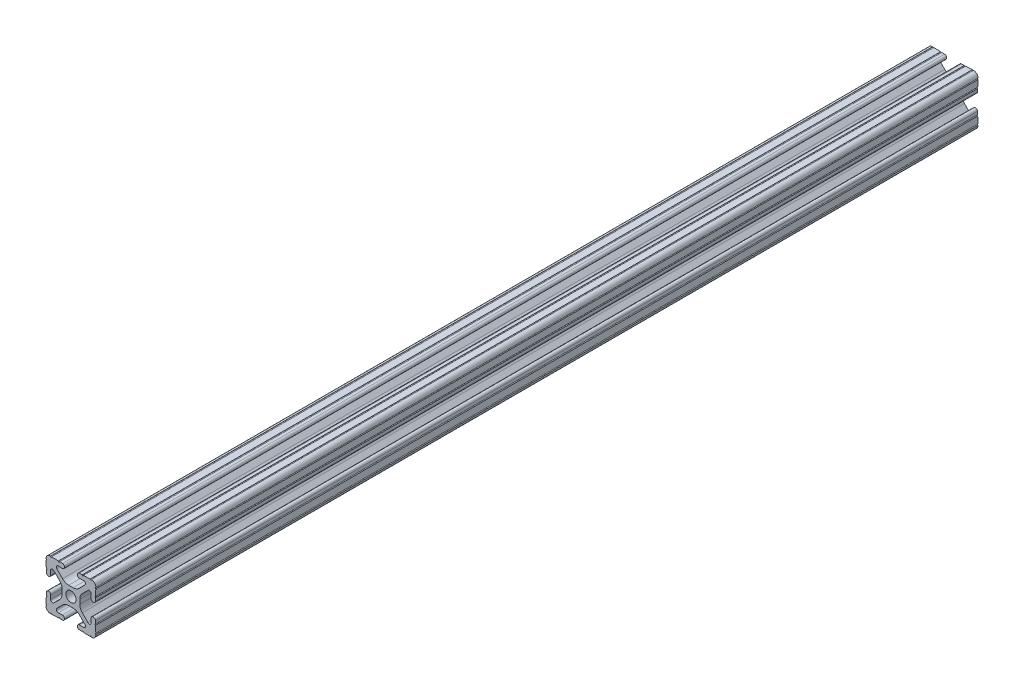
SolidWorks part; units mm, degrees
material "6063-T5"
ref_plane "Front Plane" through (0, 0, 0) normal (0, 0, 1) x (1, 0, 0)
ref_plane "Top Plane" through (0, 0, 0) normal (0, 1, 0) x (1, 0, 0)
ref_plane "Right Plane" through (0, 0, 0) normal (1, 0, 0) x (0, 0, -1)
sketch "Sketch1" plane through (0, 0, 0) normal (0, 0, 1) x (1, 0, 0)
  line L0 (0, 12.7) -> (-12.7814, 12.7) construction
  line L1 (-4.5085, 0) -> (-4.5085, 2.9459)
  line L2 (-6.0437, 12.5461) -> (-10.0976, 12.6876) construction
  line L3 (-11.5616, 12.4229) -> (-4.3159, 12.1699) construction
  line L4 (-6.4364, 10.3486) -> (-6.3592, 12.5571) construction
  line L6 (-2.9459, 4.5085) -> (0, 4.5085)
  line L7 (0, 0) -> (0, 12.7) construction
  line L8 (0, 0) -> (-12.7814, 0) construction
  line L9 (0.7813, 0.7813) -> (-0.7813, -0.7813) construction
  line L10 (-2.9459, 4.5085) -> (-7.1484, 8.711)
  line L11 (-4.5085, 2.9459) -> (-8.711, 7.1484)
  line L13 (0, 0) -> (-12.7814, 12.7814) construction
  line L14 (-10.4131, 12.6987) -> (-4.3048, 12.4853)
  line L15 (-4.3048, 12.4853) -> (-4.382, 10.2769) construction
  line L16 (-4.382, 10.2769) -> (-6.4364, 10.3486)
  line L17 (-12.6987, 10.4131) -> (-12.4853, 4.3048)
  line L18 (-10.2769, 4.382) -> (-10.3486, 6.4364)
  circle A0 centre (0, 0) radius 2.6035
  arc A1 (-4.382, 10.2769) -> (-4.3048, 12.4853) centre (-4.3434, 11.3811) ccw
  arc A2 (-7.1484, 8.711) -> (-6.4364, 10.3486) centre (-6.4698, 9.3896) cw
  arc A3 (-8.711, 7.1484) -> (-10.3486, 6.4364) centre (-9.3896, 6.4698) ccw
  arc A4 (-10.2769, 4.382) -> (-12.4853, 4.3048) centre (-11.3811, 4.3434) cw
  arc A5 (-10.4131, 12.6987) -> (-12.6987, 10.4131) centre (-10.4902, 10.4902) ccw
  arc A6 (-10.4131, 12.6987) -> (-9.7821, 12.6766) centre (-10.0976, 12.6876) ccw
  arc A7 (-6.3592, 12.5571) -> (-5.7282, 12.5351) centre (-6.0437, 12.5461) ccw
  arc A8 (-12.5571, 6.3592) -> (-12.5351, 5.7282) centre (-12.5461, 6.0437) cw
  arc A9 (-12.6987, 10.4131) -> (-12.6766, 9.7821) centre (-12.6876, 10.0976) cw
  dimension "D1" = 5.207
  dimension "D5" = 14.859
  dimension "D9" = 2
  dimension "D2" = 25.4
  dimension "D12" = 0.6314
  dimension "D10" = 2.2098
  dimension "D3" = 9.017
  dimension "D4" = 9.017
  dimension "D6" = 25.4
  dimension "D7" = 6.477
  dimension "D8" = 2.2098
  dimension "D11" = 12.7
sketch "Sketch3" plane through (0, 0, 0) normal (0, 0, 1) x (1, 0, 0)
  line L0 (-2.9459, 4.5085) -> (0, 4.5085) construction
  line L1 (-2.9459, 4.5085) -> (-7.1484, 8.711) construction
  line L2 (-4.382, 10.2769) -> (-6.4364, 10.3486) construction
  line L3 (-10.4131, 12.6987) -> (-4.3048, 12.4853) construction
  line L4 (-4.5085, 0) -> (-4.5085, 2.9459) construction
  line L5 (-4.5085, 2.9459) -> (-8.711, 7.1484) construction
  line L6 (-10.2769, 4.382) -> (-10.3486, 6.4364) construction
  line L7 (-12.6987, 10.4131) -> (-12.4853, 4.3048) construction
  line L8 (-1.1153, 4.5085) -> (1.1153, 4.5085)
  line L9 (-4.2404, 5.803) -> (-7.1484, 8.711)
  line L10 (-4.382, 10.2769) -> (-6.4364, 10.3486)
  line L11 (-9.7821, 12.6766) -> (-6.3592, 12.5571)
  line L12 (-4.5085, -1.1153) -> (-4.5085, 1.1153)
  line L13 (-5.803, 4.2404) -> (-8.711, 7.1484)
  line L14 (-10.2769, 4.382) -> (-10.3486, 6.4364)
  line L15 (-12.6766, 9.7821) -> (-12.5571, 6.3592)
  line L16 (-5.7282, 12.5351) -> (-4.3048, 12.4853)
  line L17 (-12.5351, 5.7282) -> (-12.4853, 4.3048)
  line L18 (0, 0) -> (0, 12.7) construction
  line L19 (0, 0) -> (-12.7814, 0) construction
  line L20 (12.5351, 5.7282) -> (12.4853, 4.3048)
  line L21 (5.7282, 12.5351) -> (4.3048, 12.4853)
  line L22 (12.6766, 9.7821) -> (12.5571, 6.3592)
  line L23 (10.2769, 4.382) -> (10.3486, 6.4364)
  line L24 (5.803, 4.2404) -> (8.711, 7.1484)
  line L25 (4.5085, -1.1153) -> (4.5085, 1.1153)
  line L26 (9.7821, 12.6766) -> (6.3592, 12.5571)
  line L27 (4.382, 10.2769) -> (6.4364, 10.3486)
  line L28 (4.2404, 5.803) -> (7.1484, 8.711)
  line L29 (4.2404, -5.803) -> (7.1484, -8.711)
  line L30 (4.382, -10.2769) -> (6.4364, -10.3486)
  line L31 (9.7821, -12.6766) -> (6.3592, -12.5571)
  line L32 (5.803, -4.2404) -> (8.711, -7.1484)
  line L33 (10.2769, -4.382) -> (10.3486, -6.4364)
  line L34 (12.6766, -9.7821) -> (12.5571, -6.3592)
  line L35 (5.7282, -12.5351) -> (4.3048, -12.4853)
  line L36 (12.5351, -5.7282) -> (12.4853, -4.3048)
  line L37 (-12.5351, -5.7282) -> (-12.4853, -4.3048)
  line L38 (-5.7282, -12.5351) -> (-4.3048, -12.4853)
  line L39 (-12.6766, -9.7821) -> (-12.5571, -6.3592)
  line L40 (-10.2769, -4.382) -> (-10.3486, -6.4364)
  line L41 (-5.803, -4.2404) -> (-8.711, -7.1484)
  line L42 (-9.7821, -12.6766) -> (-6.3592, -12.5571)
  line L43 (-4.382, -10.2769) -> (-6.4364, -10.3486)
  line L44 (-4.2404, -5.803) -> (-7.1484, -8.711)
  line L45 (-1.1153, -4.5085) -> (1.1153, -4.5085)
  arc A0 (-10.4131, 12.6987) -> (-9.7821, 12.6766) centre (-10.0976, 12.6876) ccw construction
  arc A1 (-6.4364, 10.3486) -> (-7.1484, 8.711) centre (-6.4698, 9.3896) ccw construction
  arc A2 (-4.382, 10.2769) -> (-4.3048, 12.4853) centre (-4.3434, 11.3811) ccw construction
  arc A3 (-8.711, 7.1484) -> (-10.3486, 6.4364) centre (-9.3896, 6.4698) ccw construction
  arc A4 (-12.4853, 4.3048) -> (-10.2769, 4.382) centre (-11.3811, 4.3434) ccw construction
  arc A5 (-6.3592, 12.5571) -> (-5.7282, 12.5351) centre (-6.0437, 12.5461) ccw construction
  arc A6 (-10.4131, 12.6987) -> (-12.6987, 10.4131) centre (-10.4902, 10.4902) ccw construction
  arc A7 (-12.6766, 9.7821) -> (-12.6987, 10.4131) centre (-12.6876, 10.0976) ccw construction
  arc A8 (-12.5351, 5.7282) -> (-12.5571, 6.3592) centre (-12.5461, 6.0437) ccw construction
  arc A9 (-10.4131, 12.6987) -> (-9.7821, 12.6766) centre (-10.0976, 12.6876) ccw
  arc A10 (-6.4364, 10.3486) -> (-7.1484, 8.711) centre (-6.4698, 9.3896) ccw
  arc A11 (-4.382, 10.2769) -> (-4.3048, 12.4853) centre (-4.3434, 11.3811) ccw
  arc A12 (-8.711, 7.1484) -> (-10.3486, 6.4364) centre (-9.3896, 6.4698) ccw
  arc A13 (-12.4853, 4.3048) -> (-10.2769, 4.382) centre (-11.3811, 4.3434) ccw
  arc A14 (-6.3592, 12.5571) -> (-5.7282, 12.5351) centre (-6.0437, 12.5461) ccw
  arc A15 (-10.4131, 12.6987) -> (-12.6987, 10.4131) centre (-10.4902, 10.4902) ccw
  arc A16 (-12.6766, 9.7821) -> (-12.6987, 10.4131) centre (-12.6876, 10.0976) ccw
  arc A17 (-12.5351, 5.7282) -> (-12.5571, 6.3592) centre (-12.5461, 6.0437) ccw
  arc A18 (-1.1153, 4.5085) -> (-4.2404, 5.803) centre (-1.1153, 8.9281) cw
  arc A19 (4.5085, 1.1153) -> (5.803, 4.2404) centre (8.9281, 1.1153) cw
  arc A20 (1.1153, 4.5085) -> (4.2404, 5.803) centre (1.1153, 8.9281) ccw
  arc A21 (-4.5085, 1.1153) -> (-5.803, 4.2404) centre (-8.9281, 1.1153) ccw
  arc A22 (12.5351, 5.7282) -> (12.5571, 6.3592) centre (12.5461, 6.0437) cw
  arc A23 (12.6766, 9.7821) -> (12.6987, 10.4131) centre (12.6876, 10.0976) cw
  arc A24 (10.4131, 12.6987) -> (12.6987, 10.4131) centre (10.4902, 10.4902) cw
  arc A25 (6.3592, 12.5571) -> (5.7282, 12.5351) centre (6.0437, 12.5461) cw
  arc A26 (12.4853, 4.3048) -> (10.2769, 4.382) centre (11.3811, 4.3434) cw
  arc A27 (8.711, 7.1484) -> (10.3486, 6.4364) centre (9.3896, 6.4698) cw
  arc A28 (4.382, 10.2769) -> (4.3048, 12.4853) centre (4.3434, 11.3811) cw
  arc A29 (6.4364, 10.3486) -> (7.1484, 8.711) centre (6.4698, 9.3896) cw
  arc A30 (10.4131, 12.6987) -> (9.7821, 12.6766) centre (10.0976, 12.6876) cw
  arc A31 (10.4131, -12.6987) -> (9.7821, -12.6766) centre (10.0976, -12.6876) ccw
  arc A32 (6.4364, -10.3486) -> (7.1484, -8.711) centre (6.4698, -9.3896) ccw
  arc A33 (4.382, -10.2769) -> (4.3048, -12.4853) centre (4.3434, -11.3811) ccw
  arc A34 (8.711, -7.1484) -> (10.3486, -6.4364) centre (9.3896, -6.4698) ccw
  arc A35 (12.4853, -4.3048) -> (10.2769, -4.382) centre (11.3811, -4.3434) ccw
  arc A36 (6.3592, -12.5571) -> (5.7282, -12.5351) centre (6.0437, -12.5461) ccw
  arc A37 (10.4131, -12.6987) -> (12.6987, -10.4131) centre (10.4902, -10.4902) ccw
  arc A38 (12.6766, -9.7821) -> (12.6987, -10.4131) centre (12.6876, -10.0976) ccw
  arc A39 (12.5351, -5.7282) -> (12.5571, -6.3592) centre (12.5461, -6.0437) ccw
  arc A40 (-4.5085, -1.1153) -> (-5.803, -4.2404) centre (-8.9281, -1.1153) cw
  arc A41 (1.1153, -4.5085) -> (4.2404, -5.803) centre (1.1153, -8.9281) cw
  arc A42 (4.5085, -1.1153) -> (5.803, -4.2404) centre (8.9281, -1.1153) ccw
  arc A43 (-1.1153, -4.5085) -> (-4.2404, -5.803) centre (-1.1153, -8.9281) ccw
  arc A44 (-12.5351, -5.7282) -> (-12.5571, -6.3592) centre (-12.5461, -6.0437) cw
  arc A45 (-12.6766, -9.7821) -> (-12.6987, -10.4131) centre (-12.6876, -10.0976) cw
  arc A46 (-10.4131, -12.6987) -> (-12.6987, -10.4131) centre (-10.4902, -10.4902) cw
  arc A47 (-6.3592, -12.5571) -> (-5.7282, -12.5351) centre (-6.0437, -12.5461) cw
  arc A48 (-12.4853, -4.3048) -> (-10.2769, -4.382) centre (-11.3811, -4.3434) cw
  arc A49 (-8.711, -7.1484) -> (-10.3486, -6.4364) centre (-9.3896, -6.4698) cw
  arc A50 (-4.382, -10.2769) -> (-4.3048, -12.4853) centre (-4.3434, -11.3811) cw
  arc A51 (-6.4364, -10.3486) -> (-7.1484, -8.711) centre (-6.4698, -9.3896) cw
  arc A52 (-10.4131, -12.6987) -> (-9.7821, -12.6766) centre (-10.0976, -12.6876) cw
  circle A53 centre (0, 0) radius 2.6035 construction
  circle A54 centre (0, 0) radius 2.6035
  point P135 (4.5085, 0)
  dimension "D2" = 4.4196
extrude "Extrude1" add sketch "Sketch3" along normal mid plane 1219.2
sketch "Sketch5" plane through (-0.4302, 12.32, 0) normal (-0.0349, 0.9994, 0) x (0.9994, 0.0349, 0)
  line L1 (28.1126, 609.6) -> (-21.2511, 609.6)
  line L2 (28.1126, 609.6) -> (28.1126, -160)
  line L3 (28.1126, -160) -> (-21.2511, -160)
  line L4 (-21.2511, 609.6) -> (-21.2511, -160)
  dimension "D1" = 769.6
  dimension "D2" = 0
extrude "Cut-Extrude1" cut sketch "Sketch5" against normal blind 60 and the other way blind 10
equation "\"D10@Sketch1\" = \"D8@Sketch1\""
equation "\"D11@Sketch1\" = \"D6@Sketch1\"/2"
equation "\"D12@Sketch1\" = \"D8@Sketch1\"/3.5"
equation "\"D2@Sketch3\" = \"D8@Sketch1\"*2"
